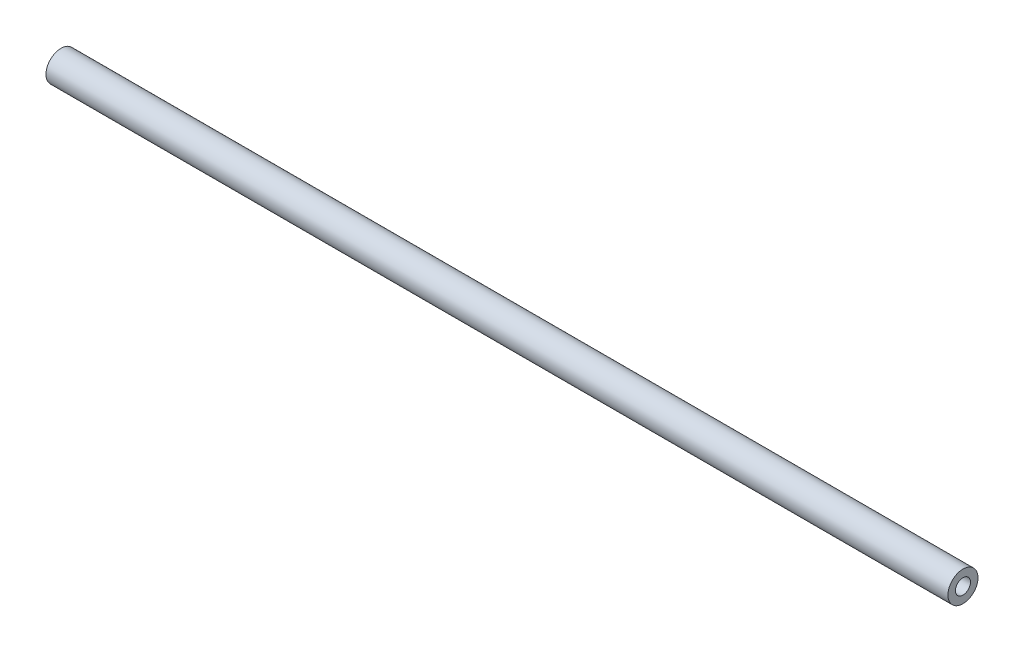
SolidWorks part; units mm, degrees
material "6061-T6 (SS)"
ref_plane "Front Plane" through (0, 0, 0) normal (0, 0, 1) x (1, 0, 0)
ref_plane "Top Plane" through (0, 0, 0) normal (0, 1, 0) x (1, 0, 0)
ref_plane "Right Plane" through (0, 0, 0) normal (1, 0, 0) x (0, 0, -1)
sketch "Sketch1" plane through (0, 0, 0) normal (1, 0, 0) x (0, 0, -1)
  circle A0 centre (0, 0) radius 6.35
  dimension "D1" = 12.7
extrude "Boss-Extrude1" add sketch "Sketch1" along normal blind 381
sketch "Sketch2" plane through (381, 0, 0) normal (1, 0, 0) x (0, 0, -1)
  circle A0 centre (0, 0) radius 3.175
  dimension "D1" = 6.35
extrude "Cut-Extrude1" cut sketch "Sketch2" against normal through all
ref_plane "Plane1" through (190.5, 0, 0) normal (1, 0, 0) x (0, 0, -1)
